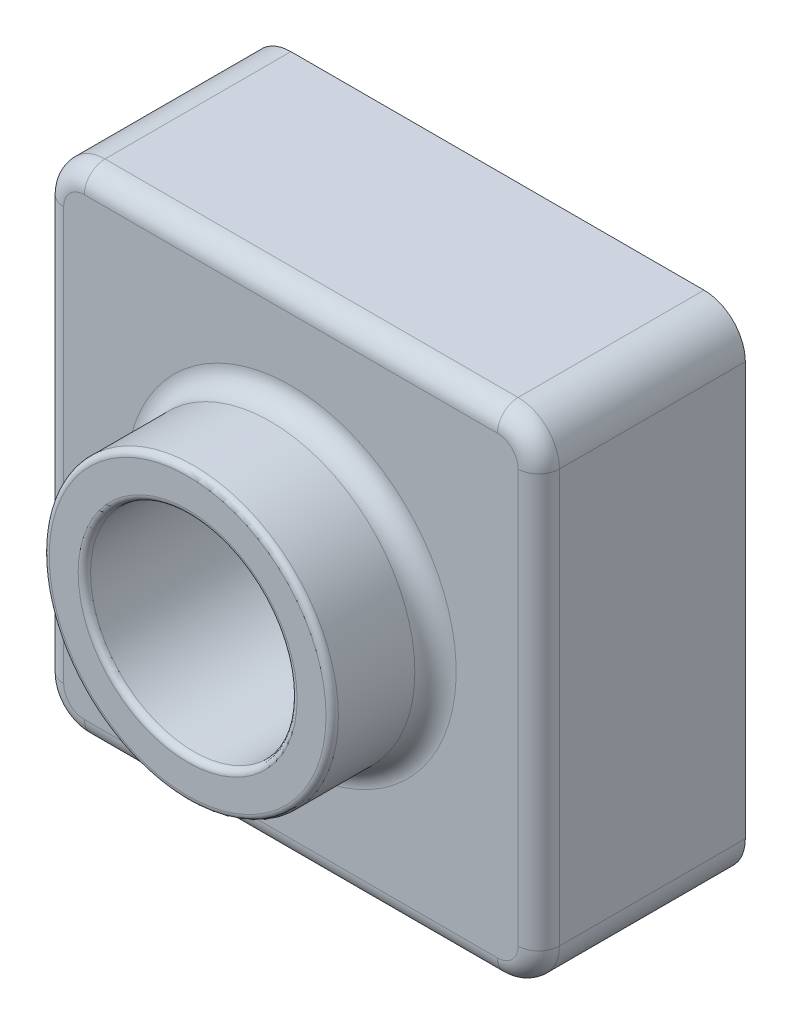
SolidWorks part; units mm, degrees
material "Chrome Stainless Steel"
ref_plane "Front Plane" through (0, 0, 0) normal (0, 0, 1) x (1, 0, 0)
ref_plane "Top Plane" through (0, 0, 0) normal (0, 1, 0) x (1, 0, 0)
ref_plane "Right Plane" through (0, 0, 0) normal (1, 0, 0) x (0, 0, -1)
sketch "Sketch2" plane through (0, 0, 0) normal (0, 0, 1) x (1, 0, 0)
  line L1 (0, 0) -> (120, 0)
  line L2 (0, 0) -> (0, 120)
  line L3 (0, 120) -> (120, 120)
  line L4 (120, 0) -> (120, 120)
  dimension "D1" = 120
  dimension "D2" = 120
extrude "Boss-Extrude1" add sketch "Sketch2" along normal blind 50
sketch "Sketch4" plane through (0, 0, 50) normal (0, 0, 1) x (1, 0, 0)
  line L0 (120, 120) -> (0, 120) construction
  line L1 (0, 120) -> (0, 0) construction
  circle A0 centre (60, 60) radius 35
  dimension "D1" = 60
  dimension "D3" = 70
  dimension "D2" = 60
extrude "Boss-Extrude2" add sketch "Sketch4" along normal blind 25
sketch "Sketch6" plane through (0, 0, 75) normal (0, 0, 1) x (1, 0, 0)
  circle A0 centre (60, 60) radius 25
  dimension "D1" = 50
extrude "Cut-Extrude1" cut sketch "Sketch6" against normal through all
fillet "Fillet1" radius 10 4 edges at (0, 120, 25) (0, 0, 25) (120, 0, 25) (120, 120, 25)
fillet "Fillet2" radius 1.5 2 edges at (95, 60, 75) (85, 60, 75)
fillet "Fillet3" radius 5 9 edges at (25, 60, 50) (117.0711, 117.0711, 50) (120, 60, 50) (117.0711, 2.9289, 50) (60, 0, 50) (2.9289, 2.9289, 50) (0, 60, 50) (2.9289, 117.0711, 50) (60, 120, 50)
shell "Shell1" thickness 2
